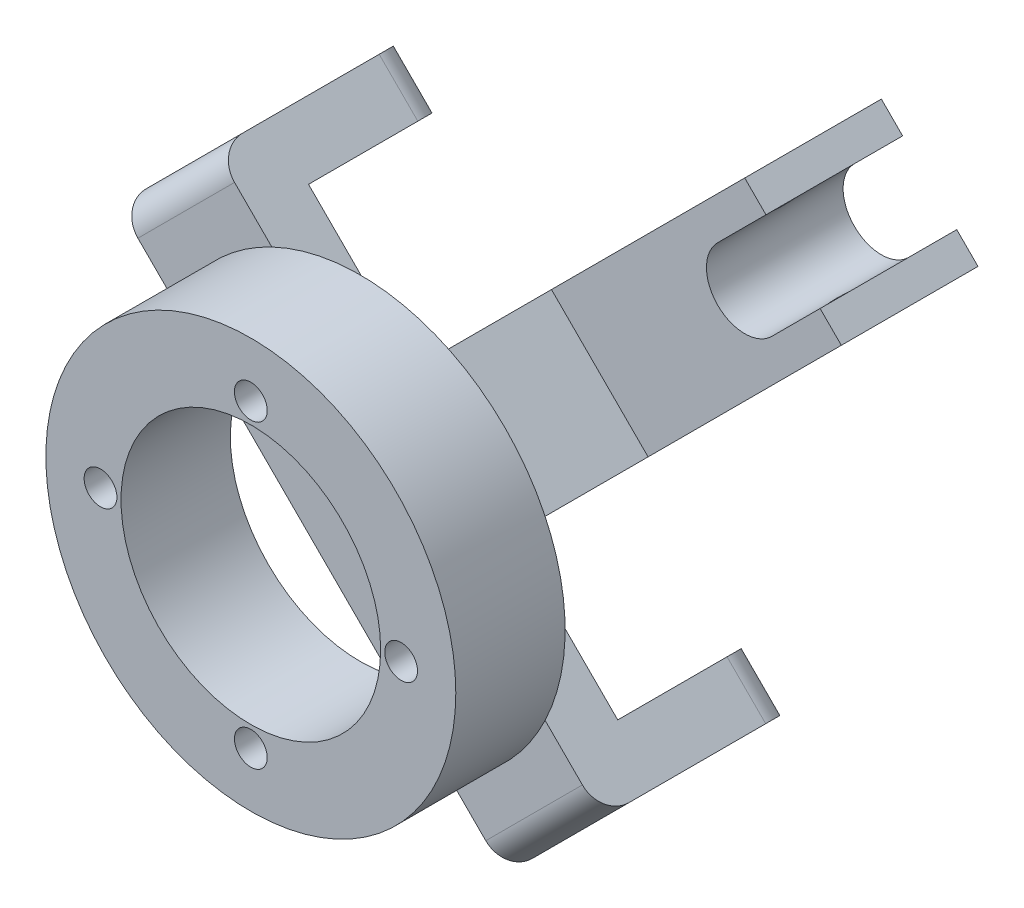
SolidWorks part; units mm, degrees
ref_plane "Płaszczyzna przednia" through (0, 0, 0) normal (0, 0, 1) x (1, 0, 0)
ref_plane "Płaszczyzna górna" through (0, 0, 0) normal (0, 1, 0) x (1, 0, 0)
ref_plane "Płaszczyzna prawa" through (0, 0, 0) normal (1, 0, 0) x (0, 0, -1)
sketch "Szkic1" plane through (0, 0, 0) normal (0, 0, 1) x (1, 0, 0)
  circle A0 centre (0, 0) radius 75
  dimension "D1" = 150
extrude "Dodanie-wyciągnięcie1" add sketch "Szkic1" along normal blind 40
sketch "Szkic2" plane through (0, 0, 40) normal (0, 0, 1) x (1, 0, 0)
  circle A0 centre (-55, 0) radius 6
  circle A1 centre (0, 55) radius 6
  circle A2 centre (55, 0) radius 6
  circle A3 centre (0, -55) radius 6
  point P12 (0, 0)
  dimension "D1" = 12
  dimension "D2" = 55
  dimension "D3" = 4
extrude "Wytnij-wyciągnięcie1" cut sketch "Szkic2" against normal blind 40
sketch "Szkic3" plane through (0, 0, 40) normal (0, 0, 1) x (1, 0, 0)
  circle A0 centre (0, 0) radius 47.5
  dimension "D1" = 95
extrude "Wytnij-wyciągnięcie2" cut sketch "Szkic3" against normal blind 40
ref_plane "Płaszczyzna1" through (0, 0, 0) normal (0.7071, -0.7071, 0) x (-0.7071, -0.7071, 0)
sketch "Szkic4" plane through (0, 0, 0) normal (0.7071, -0.7071, 0) x (-0.7071, -0.7071, 0)
  line L0 (75, 0) -> (-75, 0) construction
  line L1 (-25, 0) -> (25, 0)
  line L2 (-25, 0) -> (-25, 20)
  line L3 (-25, 20) -> (25, 20)
  line L4 (25, 0) -> (25, 20)
  dimension "D1" = 25
  dimension "D2" = 50
  dimension "D3" = 20
extrude "Dodanie-wyciągnięcie2" add sketch "Szkic4" along normal mid plane 200
sketch "Szkic6" plane through (70.7107, -70.7107, 0) normal (0.7071, -0.7071, 0) x (0, 0, -1)
  line L1 (20, 25) -> (70, 25)
  line L2 (20, 25) -> (20, -24.9998)
  line L3 (20, -24.9998) -> (70, -24.9998)
  line L4 (70, 25) -> (70, -24.9998)
  dimension "D1" = 50
extrude "Dodanie-wyciągnięcie3" add sketch "Szkic6" against normal blind 20
mirror "Lustro1" about plane through (0, 0, 0) normal (0.7071, -0.7071, 0) of "Dodanie-wyciągnięcie3"
sketch "Szkic7" plane through (-70.7107, 70.7107, 0) normal (-0.7071, 0.7071, 0) x (0, 0, 1)
  line L0 (-70, -24.9998) -> (-70, 25) construction
  circle A0 centre (-45, 0) radius 7
  dimension "D1" = 14
  dimension "D2" = 25
extrude "Wytnij-wyciągnięcie3" cut sketch "Szkic7" against normal through all
fillet "Zaokrąglenie1" radius 10 4 edges at (45.9621, -81.3171, -70) (81.3173, -45.9619, -70) (-45.9619, 81.3173, -70) (-81.3171, 45.9621, -70)
fillet "Zaokrąglenie2" radius 10 2 edges at (-70.7107, 70.7107, 0) (70.7107, -70.7107, 0)
sketch "Szkic8" plane through (0, 0, -20) normal (0, 0, -1) x (-1, 0, 0)
  line L0 (0, 35.3553) -> (35.3553, 0)
  line L1 (0, 60.5) -> (0, -60.5) construction
  line L2 (60.5, 0) -> (-60.5, 0) construction
  line L3 (35.3553, 0) -> (0, -35.3553)
  line L4 (-53.033, -88.3883) -> (88.3883, 53.033) construction
  line L5 (0, -35.3553) -> (-35.3553, 0)
  line L6 (-35.3553, 0) -> (0, 35.3553)
  dimension "D1" = 50
  dimension "D2" = 50
extrude "Dodanie-wyciągnięcie4" add sketch "Szkic8" along normal blind 100
sketch "Szkic10" plane through (17.6777, 17.6777, 0) normal (0.7071, 0.7071, 0) x (0, 0, -1)
  line L0 (120, -25) -> (20, -25) construction
  line L1 (120, 25) -> (70, 25)
  line L2 (120, 25) -> (120, -25)
  line L3 (120, -25) -> (70, -25)
  line L4 (70, 25) -> (70, -25)
  dimension "D1" = 50
extrude "Dodanie-wyciągnięcie5" add sketch "Szkic10" along normal blind 100
sketch "Szkic12" plane through (17.6777, -17.6777, 0) normal (0.7071, -0.7071, 0) x (0, 0, -1)
  line L1 (70, 125) -> (70, 25) construction
  line L4 (70, 125) -> (120, 125) construction
  circle A0 centre (95, 105) radius 7
  dimension "D3" = 14
  dimension "D1" = 25
  dimension "D2" = 20
extrude "Wytnij-wyciągnięcie5" cut sketch "Szkic12" against normal through all
sketch "Szkic14" plane through (0, 0, -120) normal (0, 0, -1) x (-1, 0, 0)
  line L0 (-38.8909, 38.8909) -> (38.8909, -38.8909) construction
  line L1 (-106.066, 70.7107) -> (-70.7107, 106.066) construction
  line L3 (35.3553, 0) -> (-70.7107, 106.066) construction
  line L7 (-80.6102, 60.8112) -> (-98.2878, 78.4889)
  line L10 (-60.8112, 80.6102) -> (-78.4889, 98.2878)
  line L11 (-78.4889, 98.2878) -> (-98.2878, 78.4889)
  arc A0 (-80.6102, 60.8112) -> (-60.8112, 80.6102) centre (-70.7107, 70.7107) ccw
  dimension "D1" = 28
  dimension "D2" = 25
  dimension "D3" = 25
extrude "Wytnij-wyciągnięcie6" cut sketch "Szkic14" against normal through all
